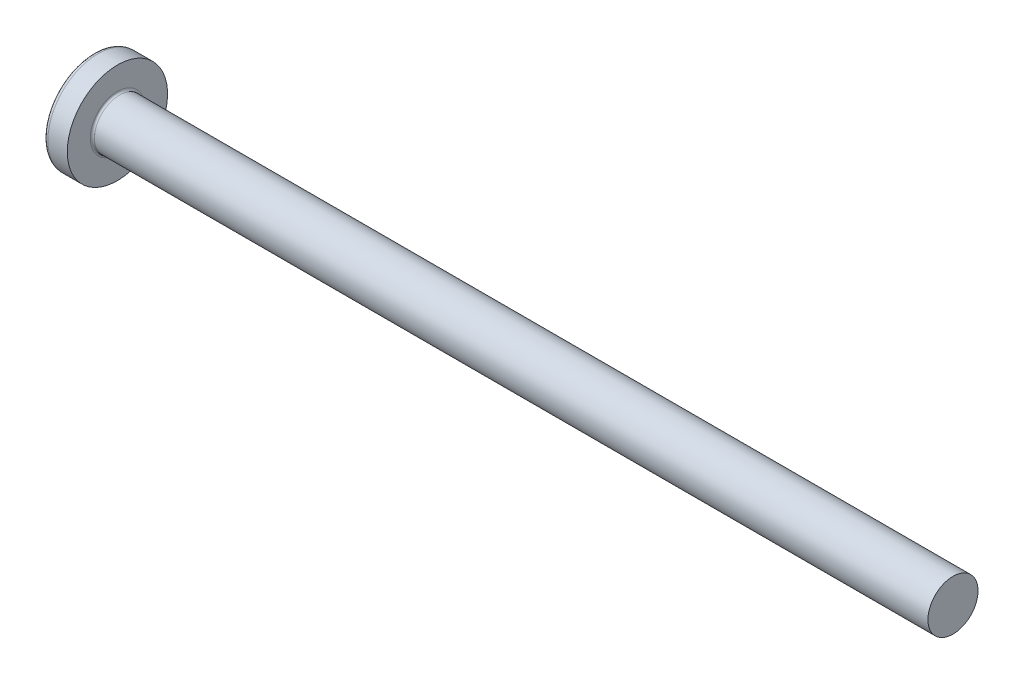
SolidWorks part; units mm, degrees
ref_plane "Plane1" through (0, 0, 0) normal (0, 0, 1) x (1, 0, 0)
ref_plane "Plane2" through (0, 0, 0) normal (0, 1, 0) x (1, 0, 0)
ref_plane "Plane3" through (0, 0, 0) normal (1, 0, 0) x (0, 0, -1)
sketch "BodySke" plane through (0, 0, 0) normal (0, 0, 1) x (1, 0, 0)
  line L0 (4.6, 3) -> (4.6, 6)
  line L1 (5.1, 6.35) -> (5.1, -3.175) construction
  line L2 (-25.4, 0) -> (127, 0) construction
  line L3 (104.6, 0) -> (0, 0)
  line L4 (4.6, 3) -> (104.6, 3)
  line L5 (104.6, 3) -> (104.6, 0)
  line L6 (2.2747, 6) -> (4.6, 6)
  line L8 (66.6, 6.35) -> (66.6, -3.175) construction
  arc A0 (1.8337, 5.7717) -> (0, 0) centre (10, 0) ccw
  arc A2 (1.8337, 5.7717) -> (2.2747, 6) centre (2.2747, 5.46) cw
  dimension "Head_crown_rad" = 10
  dimension "Head_fillet_rad" = 0.54
  dimension "Length" = 100
  dimension "Head_ht" = 4.6
  dimension "Head_dia" = 12
  dimension "Advance" = 1
  dimension "Thread_nom" = 38
  dimension "Diameter" = 6
revolve "Base-Revolve" add sketch "BodySke"
cosmetic thread "ThreadCosmetic" [suppressed]
fillet "Fillet1" radius 0.25 1 edges at (4.6, 0, 3)
sketch "Sketch3" plane through (0, 0, 0) normal (1, 0, 0) x (0, 0, -1)
  line L0 (0.71, -3.35) -> (-0.71, -3.35)
  line L1 (0.71, -3.35) -> (0.71, 3.35)
  line L2 (-0.71, 3.35) -> (0.71, 3.35)
  line L3 (-0.71, 3.35) -> (-0.71, -3.35)
  dimension "Cross_dia" = 6.7
  dimension "D1" = 3.35
  dimension "Cross_width" = 1.42
  dimension "D2" = 0.71
ref_plane "Plane4" through (3.46, 0, 0) normal (1, 0, 0) x (0, 0, -1)
sketch "Sketch4" plane through (3.46, 0, 0) normal (1, 0, 0) x (0, 0, -1)
  line L0 (0.71, -1.6249) -> (-0.71, -1.6249)
  line L1 (0.71, -1.6249) -> (0.71, 1.6249)
  line L2 (-0.71, 1.6249) -> (0.71, 1.6249)
  line L3 (-0.71, 1.6249) -> (-0.71, -1.6249)
  dimension "D1" = 1.42
  dimension "D2" = 3.2498
  dimension "D3" = 0.71
  dimension "D4" = 1.6249
loft "Recess" cut profiles "Sketch3", "Sketch4"
pattern_circular "RecPat" count 2 every 90 about axis through (0, 0, 0) along (1, 0, 0) of "Recess"
sketch "RecCorSke" plane through (0, 0, 0) normal (0, 0, 1) x (1, 0, 0)
  line L0 (-3.175, 0) -> (15.875, 0) construction
  line L1 (-25.4, 0) -> (127, 0) construction
  line L2 (0, 0) -> (0, 1.5224)
  line L3 (0, 1.5224) -> (3.46, 1.2805)
  line L4 (3.46, 1.2805) -> (3.8761, 0)
  line L5 (3.8761, 0) -> (0, 0)
  dimension "Diameter" = 2.561
  dimension "Depth" = 3.46
  dimension "Draft_angle" = 4
  dimension "Bottom_angle" = 18
revolve "RecessCore" cut sketch "RecCorSke" angle 360 about L0
sketch "ThdSchSke" plane through (0, 0, 0) normal (0, 0, 1) x (1, 0, 0)
  line L0 (66.6, -2.4455) -> (66.2117, -3)
  line L1 (66.6, -2.4455) -> (66.9883, -3)
  line L2 (66.9883, -3) -> (66.9883, -3.75)
  line L3 (-3.175, 0) -> (5.1513, 0) construction
  line L5 (66.9883, -3.75) -> (66.2117, -3.75)
  line L6 (66.2117, -3.75) -> (66.2117, -3)
  dimension "Diameter" = 6
  dimension "SideAngle" = 55
  dimension "VeeAngle" = 70
  dimension "Thread_minor" = 4.891
  dimension "Overcut" = 7.5
  dimension "Start" = 66.6
revolve "ThreadSchematic" [suppressed] cut sketch "ThdSchSke" angle 360 about L3
pattern_linear "ThdSchPat" [suppressed]
equation "\"D1@Sketch3\" = \"Cross_dia@Sketch3\" / 2"
equation "\"D2@Sketch3\" = \"Cross_width@Sketch3\" / 2"
equation "\"Depth@RecCorSke\" = \"Cross_depth@Plane4\""
equation "\"D1@Sketch4\" = \"Cross_width@Sketch3\""
equation "\"D2@Sketch4\" = \"Cross_dia@Sketch3\" - 2.0 * \"Cross_depth@Plane4\" * tan(26.5  * 0.017453292)"
equation "\"D3@Sketch4\" = \"D1@Sketch4\" / 2"
equation "\"D4@Sketch4\" = \"D2@Sketch4\" / 2"
equation "\"Thread_length@ThreadCosmetic\" = ((sgn( (\"Length@BodySke\" - \"Advance@BodySke\" * 2.0 ) - \"Thread_nom@BodySke\" )-1)*( (\"Length@BodySke\" - \"Advance@BodySke\" * 2.0 ) - \"Thread_nom@BodySke\" ))/-2+ \"Thread_nom@BodySke\""
equation "\"Thread_minor@ThdSchSke\" = \"Thread_minor@ThreadCosmetic\""
equation "\"Diameter@ThdSchSke\" = \"Diameter@BodySke\""
equation "\"Overcut@ThdSchSke\" = \"Diameter@BodySke\" * 1.25"
equation "\"Start@ThdSchSke\" = \"Head_ht@BodySke\" + \"Length@BodySke\" - \"Thread_length@ThreadCosmetic\"  '---Non-countersunk---"
equation "\"Num_threads@ThdSchPat\" = int( \"Thread_length@ThreadCosmetic\" / \"Advance@BodySke\" + 0.999 )  + 1"
equation "\"Advance@ThdSchPat\" = \"Thread_length@ThreadCosmetic\" /  (\"Num_threads@ThdSchPat\" - 1) 'relax it"
